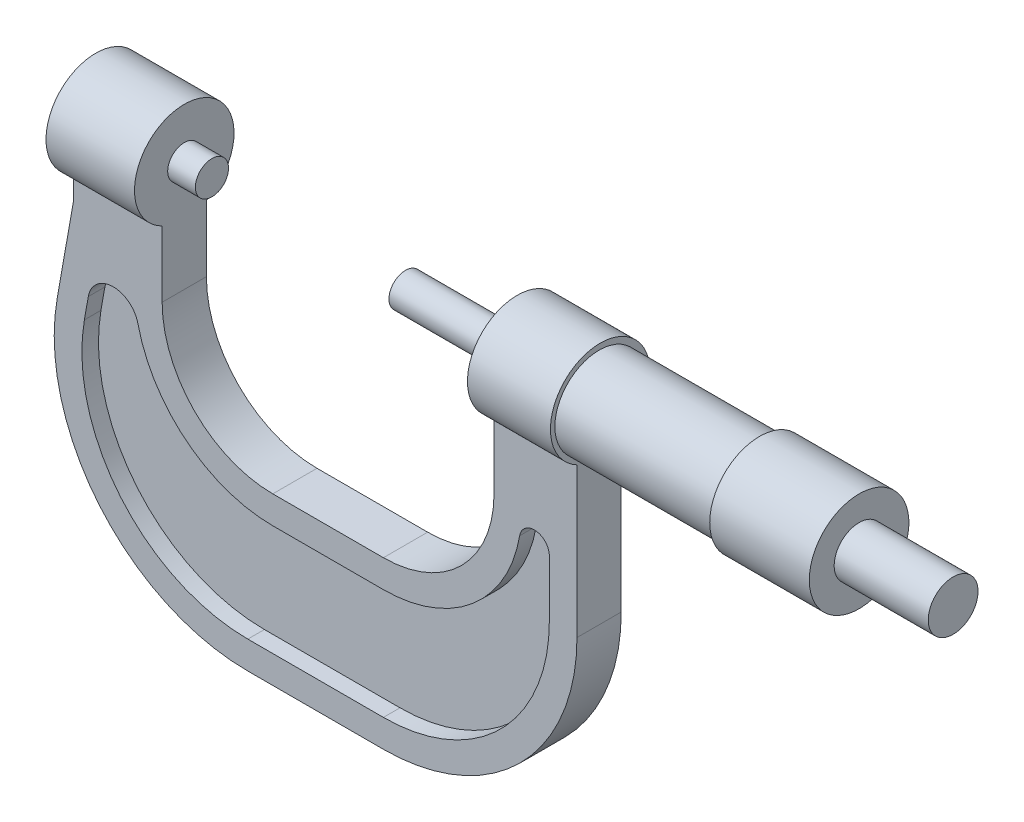
SolidWorks part; units mm, degrees
material "1060 Alloy"
ref_plane "Front Plane" through (0, 0, 0) normal (1, 0, 0) x (0, 1, 0)
ref_plane "Top Plane" through (0, 0, 0) normal (0, 0, 1) x (0, 1, 0)
ref_plane "Right Plane" through (0, 0, 0) normal (0, 1, 0) x (-1, 0, 0)
sketch "Sketch2" plane through (0, 0, 0) normal (1, 0, 0) x (0, 1, 0)
  circle A0 centre (0, 0) radius 4.5
  dimension "D1" = 9
extrude "Boss-Extrude1" add sketch "Sketch2" along normal blind 17
sketch "Sketch3" plane through (0, 0, 0) normal (-1, 0, 0) x (0, -1, 0)
  circle A0 centre (0, 0) radius 9
  dimension "D1" = 18
extrude "Boss-Extrude2" add sketch "Sketch3" along normal blind 18
sketch "Sketch4" plane through (-18, 0, 0) normal (-1, 0, 0) x (0, -1, 0)
  circle A0 centre (0, 0) radius 8
  dimension "D1" = 16
extrude "Boss-Extrude3" add sketch "Sketch4" along normal blind 29
sketch "Sketch5" plane through (-47, 0, 0) normal (-1, 0, 0) x (0, -1, 0)
  circle A0 centre (0, -0.1979) radius 9
  dimension "D1" = 18
extrude "Boss-Extrude4" add sketch "Sketch5" along normal blind 15
sketch "Sketch6" plane through (-62, 0, 0) normal (-1, 0, 0) x (0, -1, 0)
  circle A0 centre (0, 0) radius 3
  dimension "D1" = 6
extrude "Boss-Extrude5" add sketch "Sketch6" along normal blind 20
sketch "Sketch16" plane through (0, 0, 0) normal (0, 0, 1) x (0, 1, 0)
  line L0 (0, 62) -> (-20, 62)
  line L1 (-40, 82) -> (-40, 102)
  line L2 (-20, 122) -> (0, 122)
  line L3 (0, 122) -> (0, 138)
  line L4 (0, 138) -> (-12, 138)
  line L5 (-12, 138) -> (-28.9223, 140.9839)
  line L7 (-70, 106.5156) -> (-70, 82)
  line L8 (-35, 47) -> (0, 47)
  line L9 (0, 47) -> (0, 62)
  line L10 (9, 62) -> (-9, 62) construction
  line L11 (3, 82) -> (-3, 82) construction
  arc A0 (-70, 82) -> (-35, 47) centre (-35, 82) ccw
  arc A1 (-28.9223, 140.9839) -> (-70, 106.5156) centre (-35, 106.5156) ccw
  arc A2 (-20, 62) -> (-40, 82) centre (-20, 82) cw
  arc A3 (-40, 102) -> (-20, 122) centre (-20, 102) cw
  point P12 (0, 130)
  point P23 (-40, 62)
  point P26 (-40, 122)
  dimension "D8" = 35
  dimension "D9" = 20
  dimension "D1" = 40
  dimension "D2" = 60
  dimension "D3" = 40
  dimension "D4" = 16
  dimension "D5" = 12
  dimension "D6" = 70
  dimension "D7" = 170
  dimension "D10" = 15
extrude "Boss-Extrude6" add sketch "Sketch16" along normal mid plane 8
ref_plane "Plane1" through (-117, 0, 0) normal (-1, 0, 0) x (0, 0, 1)
sketch "Sketch17" plane through (-117, 0, 0) normal (-1, 0, 0) x (0, 0, 1)
  circle A0 centre (0, 0) radius 3
extrude "Boss-Extrude7" add sketch "Sketch17" along normal blind 5 separate body
sketch "Sketch18" plane through (-122, 0, 0) normal (-1, 0, 0) x (0, -1, 0)
  circle A0 centre (0, 0) radius 9
  dimension "D1" = 18
extrude "Boss-Extrude8" add sketch "Sketch18" along normal blind 16
sketch "Sketch20" [suppressed] plane through (0, 0, 4) normal (0, 0, 1) x (1, 0, 0)
  line L0 (-127.0657, -19.9628) -> (-127.0657, -33.9068)
  line L1 (-127.0657, -33.9068) -> (-56.395, -33.9068)
  line L2 (-56.395, -33.9068) -> (-56.395, -18.0613)
  line L3 (-49.423, -18.0613) -> (-49.423, -42.9387)
  line L4 (-49.423, -42.9387) -> (-136.0976, -42.9387)
  line L5 (-136.0976, -42.9387) -> (-136.0976, -19.9628)
  arc A0 (-56.395, -18.0613) -> (-49.423, -18.0613) centre (-52.909, -18.0613) cw
  arc A1 (-136.0976, -19.9628) -> (-127.0657, -19.9628) centre (-131.5817, -19.9628) cw
sketch "Sketch21" plane through (0, 0, 4) normal (0, 0, 1) x (1, 0, 0)
  line L8 (-106.5156, -65) -> (-82, -65)
  line L9 (-133.076, -12.8682) -> (-136.0598, -29.7906)
  line L10 (-106.5156, -65) -> (-82, -65)
  line L11 (-135.3539, -25.7868) -> (-136.0598, -29.7906)
  line L17 (-52, -35) -> (-52, -7.961)
  line L18 (-52, -35) -> (-52, -24.7009)
  line L27 (-146.7452, -22) -> (-33.3736, -22) construction
  line L28 (-127, -20) -> (-127, -8.0623)
  line L29 (-82, -45) -> (-102, -45)
  line L30 (-57, -7.961) -> (-57, -20)
  line L32 (-82, -45) -> (-102, -45)
  arc A8 (-82, -65) -> (-52, -35) centre (-82, -35) ccw
  arc A9 (-136.0598, -29.7906) -> (-106.5156, -65) centre (-106.5156, -35) ccw
  arc A11 (-136.0598, -29.7906) -> (-106.5156, -65) centre (-106.5156, -35) ccw
  arc A12 (-135.3539, -25.7868) -> (-126.3732, -25.5629) centre (-130.8409, -26.5826) cw
  arc A13 (-57.3626, -24.2425) -> (-52, -24.7009) centre (-54.7009, -24.7009) cw
  arc A18 (-82, -65) -> (-52, -35) centre (-82, -35) ccw
  arc A19 (-82, -65) -> (-52, -35) centre (-82, -35) ccw
  arc A23 (-127, -20) -> (-102, -45) centre (-102, -20) ccw
  arc A24 (-82, -45) -> (-57, -20) centre (-82, -20) ccw
  arc A25 (-126.3732, -25.5629) -> (-102, -45) centre (-102, -20) ccw
  arc A26 (-82, -45) -> (-57.3626, -24.2425) centre (-82, -20) ccw
  dimension "D3" = 5
  dimension "D1" = 5
  dimension "D2" = 5
  dimension "D4" = 22
extrude "Cut-Extrude1" cut sketch "Sketch21" against normal blind 3
mirror "Mirror1" about plane through (0, 0, 0) normal (0, 0, 1) of "Cut-Extrude1"
